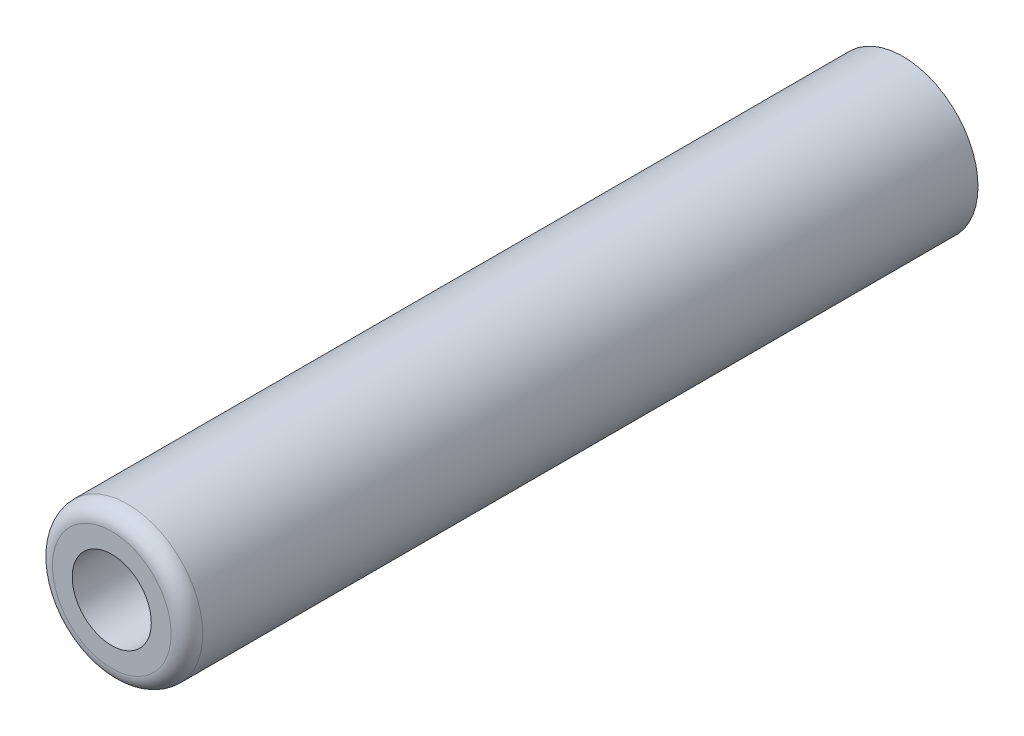
SolidWorks part; units mm, degrees
ref_plane "Front Plane" through (0, 0, 0) normal (0, 0, 1) x (1, 0, 0)
ref_plane "Top Plane" through (0, 0, 0) normal (0, 1, 0) x (1, 0, 0)
ref_plane "Right Plane" through (0, 0, 0) normal (1, 0, 0) x (0, 0, -1)
sketch "Sketch1" plane through (0, 0, 0) normal (0, 0, 1) x (1, 0, 0)
  circle A0 centre (0, 0) radius 3.8
  dimension "D1" = 7.6
extrude "Boss-Extrude1" add sketch "Sketch1" along normal mid plane 40
sketch "Sketch2" plane through (0, 0, 0) normal (0, 0, 1) x (1, 0, 0)
  circle A0 centre (0, 0) radius 2
  dimension "D1" = 4
extrude "Cut-Extrude1" cut sketch "Sketch2" against normal through all both and the other way through all
fillet "Fillet1" radius 0.8 1 edges at (3.8, 0, 20)
